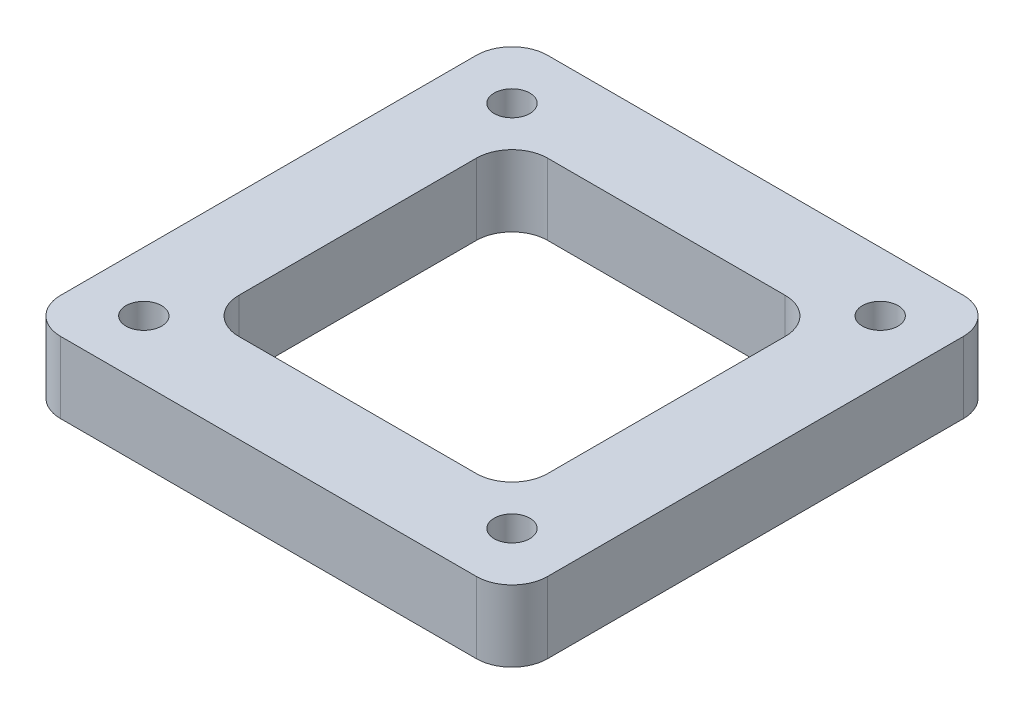
SolidWorks part; units mm, degrees
ref_plane "Front Plane" through (0, 0, 0) normal (0, 0, 1) x (1, 0, 0)
ref_plane "Top Plane" through (0, 0, 0) normal (0, 1, 0) x (1, 0, 0)
ref_plane "Right Plane" through (0, 0, 0) normal (1, 0, 0) x (0, 0, -1)
sketch "Sketch1" plane through (0, 0, 0) normal (0, 1, 0) x (1, 0, 0)
  line L1 (-20.5, 20.5) -> (20.5, 20.5)
  line L2 (-20.5, 20.5) -> (-20.5, -20.5)
  line L3 (-20.5, -20.5) -> (20.5, -20.5)
  line L4 (20.5, 20.5) -> (20.5, -20.5)
  line L5 (-20.5, 20.5) -> (20.5, -20.5) construction
  line L6 (-20.5, -20.5) -> (20.5, 20.5) construction
  point P0 (0, 0)
  dimension "D1" = 41
  dimension "D2" = 41
extrude "Boss-Extrude1" add sketch "Sketch1" along normal blind 6
sketch "Sketch2" plane through (0, 0, 0) normal (0, 1, 0) x (1, 0, 0)
  line L0 (-15.5, 15.5) -> (15.5, 15.5) construction
  line L1 (15.5, 15.5) -> (15.5, -15.5) construction
  line L2 (15.5, -15.5) -> (-15.5, -15.5) construction
  line L3 (-15.5, -15.5) -> (-15.5, 15.5) construction
  circle A0 centre (-15.5, 15.5) radius 1.5
  circle A1 centre (15.5, 15.5) radius 1.5
  circle A2 centre (-15.5, -15.5) radius 1.5
  circle A3 centre (15.5, -15.5) radius 1.5
  dimension "D1" = 3
  dimension "D2" = 3
  dimension "D3" = 3
  dimension "D4" = 3
  dimension "D5" = 31
  dimension "D6" = 31
  dimension "D7" = 31
  dimension "D8" = 31
  dimension "D9" = 15.5
  dimension "D10" = 15.5
extrude "Cut-Extrude1" cut sketch "Sketch2" along normal blind 6
sketch "Sketch3" plane through (0, 0, 0) normal (0, 1, 0) x (1, 0, 0)
  line L1 (-13, 13) -> (13, 13)
  line L2 (-13, 13) -> (-13, -13)
  line L3 (-13, -13) -> (13, -13)
  line L4 (13, 13) -> (13, -13)
  line L5 (-13, 13) -> (13, -13) construction
  line L6 (-13, -13) -> (13, 13) construction
  point P0 (0, 0)
  dimension "D1" = 26
  dimension "D2" = 26
extrude "Cut-Extrude2" cut sketch "Sketch3" along normal blind 6
fillet "Fillet1" radius 3 8 edges at (20.5, 3, -20.5) (20.5, 3, 20.5) (-20.5, 3, -20.5) (-20.5, 3, 20.5) (13, 3, -13) (13, 3, 13) (-13, 3, 13) (-13, 3, -13)
